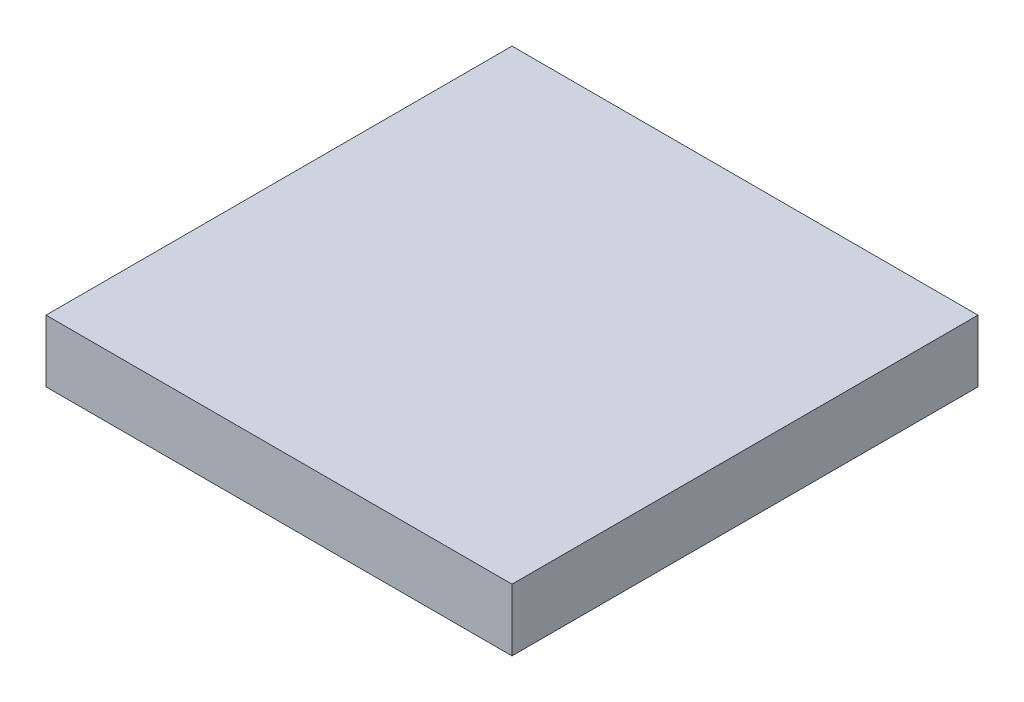
SolidWorks part; units mm, degrees
ref_plane "Front Plane" through (0, 0, 0) normal (0, 0, 1) x (1, 0, 0)
ref_plane "Top Plane" through (0, 0, 0) normal (0, 1, 0) x (1, 0, 0)
ref_plane "Right Plane" through (0, 0, 0) normal (1, 0, 0) x (0, 0, -1)
sketch "Sketch1" plane through (0, 0, 0) normal (0, 1, 0) x (1, 0, 0)
  line L1 (0, 12) -> (12, 12)
  line L2 (0, 12) -> (0, 0)
  line L3 (0, 0) -> (12, 0)
  line L4 (12, 12) -> (12, 0)
  dimension "D1" = 12
  dimension "D2" = 12
extrude "Boss-Extrude1" add sketch "Sketch1" along normal blind 1.6
sketch "Sketch2" plane through (0, 1.6, 0) normal (0, 1, 0) x (1, 0, 0)
  line L0 (0, 12) -> (0, 0) construction
  line L1 (5, 4) -> (7, 4)
  line L2 (5, 4) -> (5, 8)
  line L3 (5, 8) -> (7, 8)
  line L4 (7, 4) -> (7, 8)
  line L6 (12, 12) -> (0, 12) construction
  dimension "D1" = 4
  dimension "D2" = 2
  dimension "D3" = 5
  dimension "D4" = 4
